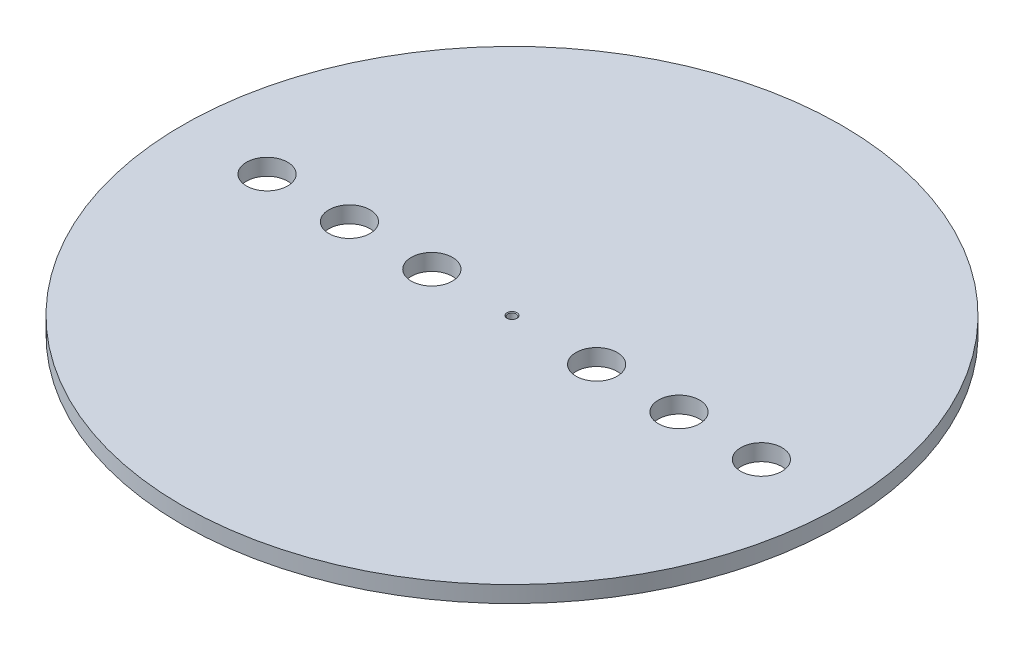
SolidWorks part; units mm, degrees
material "Chrome Stainless Steel"
ref_plane "Front Plane" through (0, 0, 0) normal (0, 0, 1) x (1, 0, 0)
ref_plane "Top Plane" through (0, 0, 0) normal (0, 1, 0) x (1, 0, 0)
ref_plane "Right Plane" through (0, 0, 0) normal (1, 0, 0) x (0, 0, -1)
sketch "Sketch1" plane through (0, 0, 0) normal (0, 1, 0) x (1, 0, 0)
  circle A0 centre (0, 0) radius 400
extrude "Boss-Extrude1" add sketch "Sketch1" along normal blind 20
sketch "Sketch2" plane through (0, 0, 0) normal (0, 1, 0) x (1, 0, 0)
  circle A1 centre (102.6987, 0) radius 25
  circle A2 centre (202.6987, 0) radius 25
  circle A3 centre (302.6987, 0) radius 25
  circle A4 centre (-97.3013, 0) radius 25
  circle A5 centre (-197.3013, 0) radius 25
  circle A6 centre (-297.3013, 0) radius 25
extrude "Cut-Extrude3" cut sketch "Sketch2" along normal blind 20
hole_wizard "M12 Tapped Hole1" positions "Sketch4" profile "Sketch5" tap size "M12" standard "GB"
sketch "Sketch4" plane through (0, 20, 0) normal (0, 1, 0) x (1, 0, 0)
  point P0 (0, 0)
sketch "Sketch5" plane through (0, 20, 0) normal (1, 0, 0) x (0, 0, 1)
  line L0 (0, 0) -> (0, 35.8144)
  line L1 (0, 35.8144) -> (5.1, 32.75)
  line L2 (5.1, 32.75) -> (5.1, 0.925)
  line L3 (5.1, 0.925) -> (6.025, 0)
  line L5 (6.025, 0) -> (0, 0)
  line L6 (-5.1, 0.925) -> (-6.025, 0) construction
  line L10 (0, 35.8144) -> (-5.1, 32.75) construction
  line L11 (0, -6.35) -> (0, 107.95) construction
  dimension "Tap Drill Dia." = 10.2
  dimension "Tap Drill Depth" = 32.75
  dimension "Near C'Sink Dia." = 12.05
  dimension "Near C'Sink Angle" = 90
  dimension "Drill Angle" = 118
cosmetic thread "Hole Thread1" parameters "D1"=20, "D2"=12
cosmetic thread "Cosmetic Thread1" parameters "D1"=5, "D2"=12
